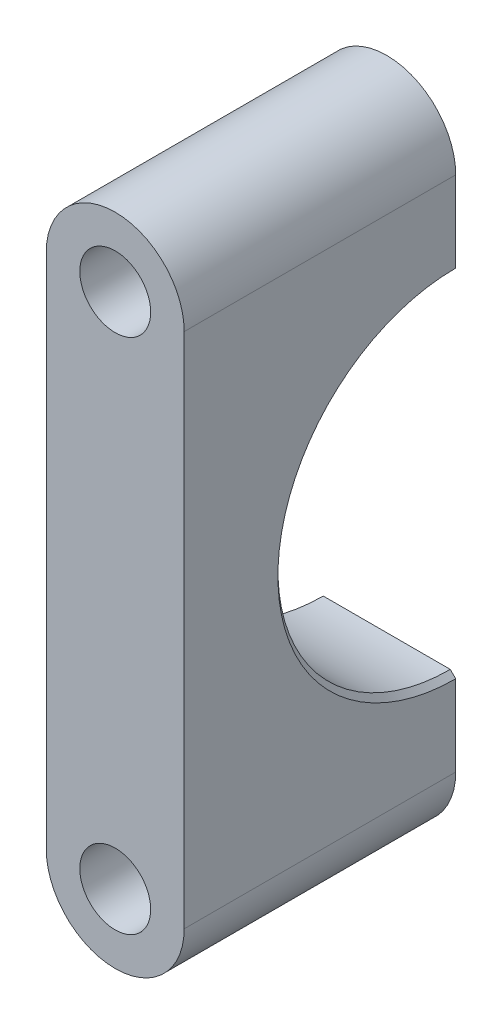
SolidWorks part; units mm, degrees
ref_plane "Front Plane" through (0, 0, 0) normal (0, 0, 1) x (1, 0, 0)
ref_plane "Top Plane" through (0, 0, 0) normal (0, 1, 0) x (1, 0, 0)
ref_plane "Right Plane" through (0, 0, 0) normal (1, 0, 0) x (0, 0, -1)
sketch "Sketch2" plane through (0, 0, 0) normal (0, 0, 1) x (1, 0, 0)
  line L2 (-6.35, 23.8125) -> (-6.35, -23.8114)
  line L4 (6.35, 23.8125) -> (6.35, -23.8114)
  arc A0 (-6.35, -23.8114) -> (6.35, -23.8114) centre (0, -23.8114) ccw
  arc A1 (6.35, 23.8125) -> (-6.35, 23.8125) centre (0, 23.8125) ccw
  circle A2 centre (0, -23.8114) radius 3.2639
  circle A3 centre (0, 23.8125) radius 3.2639
  point P0 (0, 0)
  point P6 (0, -23.8114)
  point P10 (0, 0)
  point P12 (0, 0)
  point P13 (0, -23.8114)
  point P14 (0, -23.8114)
  dimension "D3" = 12.7
  dimension "D1" = 6.5278
  dimension "D4" = 6.5278
  dimension "D2" = 12.7
extrude "Boss-Extrude1" add sketch "Sketch2" along normal blind 25.0031
sketch "Sketch3" plane through (6.35, 0, 0) normal (1, 0, 0) x (0, 0, -1)
  circle A0 centre (0, 0) radius 15.875
  dimension "D1" = 31.75
extrude "Cut-Extrude1" cut sketch "Sketch3" against normal through all
chamfer "Chamfer1" distance 0.5 angle 45 1 edges at (6.35, 0, 15.875)
chamfer "Chamfer2" distance 0.5 angle 45 1 edges at (-6.35, 0, 15.875)
